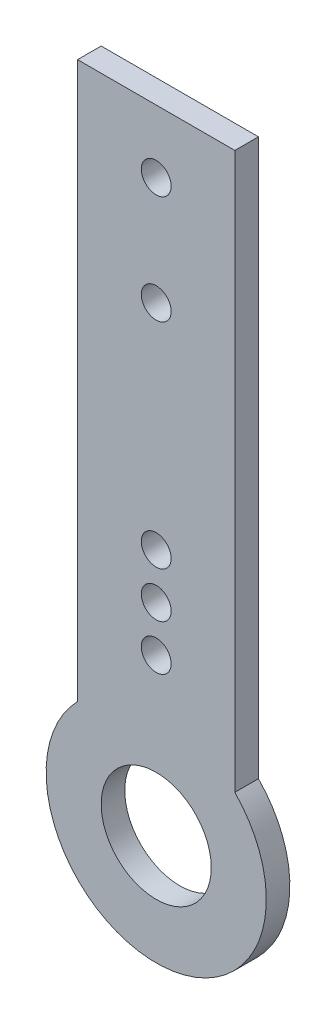
SolidWorks part; units mm, degrees
ref_plane "前视基准面" through (0, 0, 0) normal (0, 0, 1) x (1, 0, 0)
ref_plane "上视基准面" through (0, 0, 0) normal (0, 1, 0) x (1, 0, 0)
ref_plane "右视基准面" through (0, 0, 0) normal (1, 0, 0) x (0, 0, -1)
sketch "草图1" plane through (0, 0, 0) normal (0, 0, 1) x (1, 0, 0)
  line L0 (-5, 0) -> (5, 0)
  line L1 (-5, 0) -> (-5, 40.25)
  line L2 (5, 0) -> (5, 40.25)
  line L3 (-5, 40.25) -> (5, 40.25)
  circle A0 centre (0, 0) radius 3.5
  circle A1 centre (0, 0) radius 7
  circle A2 centre (0, 12.85) radius 0.95
  circle A3 centre (0, 15.75) radius 0.95
  circle A4 centre (0, 9.95) radius 0.95
  circle A5 centre (0, 36.25) radius 0.95
  circle A6 centre (0, 29.35) radius 0.95
  point P4 (0, 0)
  dimension "D1" = 7
  dimension "D2" = 14
  dimension "D5" = 1.9
  dimension "D6" = 1.9
  dimension "D7" = 1.9
  dimension "D8" = 9.95
  dimension "D9" = 2.9
  dimension "D10" = 2.9
  dimension "D11" = 1.9
  dimension "D12" = 1.9
  dimension "D13" = 4
  dimension "D14" = 6.9
  dimension "D3" = 40.25
  dimension "D4" = 10
extrude "凸台-拉伸2" add sketch "草图1" along normal blind 1.5 contours A1 L2 L3 L1 A4 A3 A2 | L1 A1 L2 L0 A0 | L2 A1 L1 L0 A0
